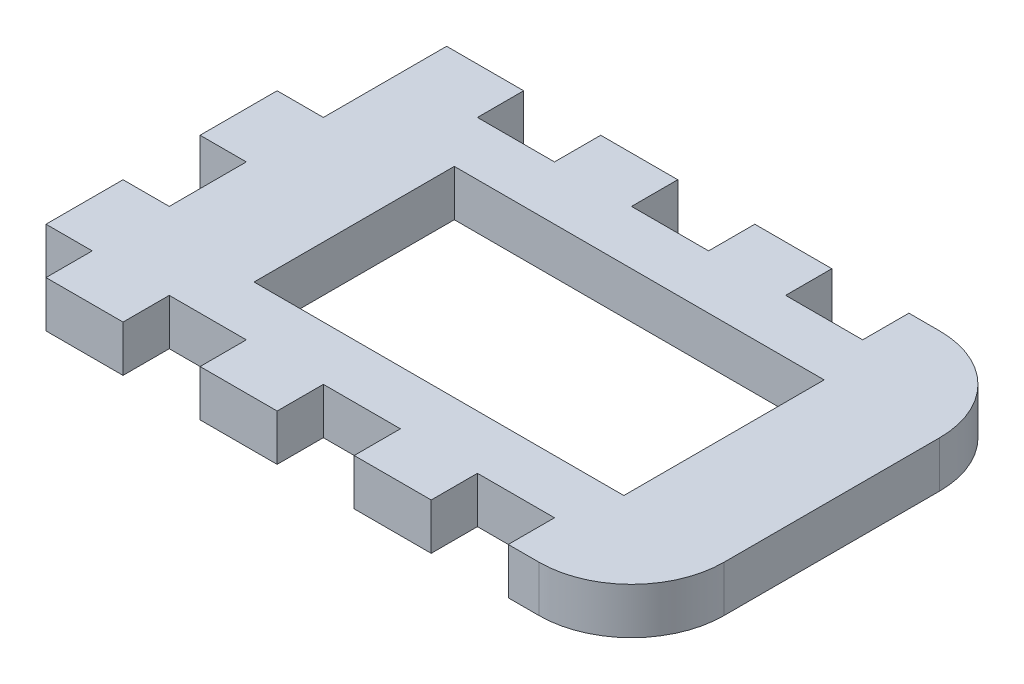
SolidWorks part; units mm, degrees
ref_plane "Front Plane" through (0, 0, 0) normal (0, 0, 1) x (1, 0, 0)
ref_plane "Top Plane" through (0, 0, 0) normal (0, 1, 0) x (1, 0, 0)
ref_plane "Right Plane" through (0, 0, 0) normal (1, 0, 0) x (0, 0, -1)
sketch "Sketch1" plane through (0, 0, 0) normal (0, 1, 0) x (1, 0, 0)
  line L1 (-19, 13) -> (19, 13)
  line L2 (-19, 13) -> (-19, -13)
  line L3 (-19, -13) -> (19, -13)
  line L4 (19, 13) -> (19, -13)
  line L5 (-19, 13) -> (19, -13) construction
  line L6 (-19, -13) -> (19, 13) construction
  point P0 (0, 0)
  dimension "D1" = 38
  dimension "D2" = 26
extrude "Boss-Extrude1" add sketch "Sketch1" along normal mid plane 3
sketch "Sketch2" plane through (0, -1.5, 0) normal (0, -1, 0) x (1, 0, 0)
  line L1 (12, -6.5) -> (-12, -6.5)
  line L2 (12, -6.5) -> (12, 6.5)
  line L3 (12, 6.5) -> (-12, 6.5)
  line L4 (-12, -6.5) -> (-12, 6.5)
  line L5 (12, -6.5) -> (-12, 6.5) construction
  line L6 (12, 6.5) -> (-12, -6.5) construction
  point P0 (0, 0)
  dimension "D1" = 24
  dimension "D2" = 13
extrude "Cut-Extrude1" cut sketch "Sketch2" against normal up to surface (3 mm away) up to face at (0, 1.5, 0)
sketch "Sketch8" plane through (-19, 0, 0) normal (-1, 0, 0) x (0, 0, 1)
  line L0 (-13, -1.5) -> (13, -1.5) construction
  line L1 (-13, 1.5) -> (-10, 1.5)
  line L2 (-13, 1.5) -> (-13, -1.5)
  line L3 (-13, -1.5) -> (-10, -1.5)
  line L4 (-10, 1.5) -> (-10, -1.5)
  line L6 (13, 1.5) -> (10, 1.5)
  line L7 (13, 1.5) -> (13, -1.5)
  line L8 (13, -1.5) -> (10, -1.5)
  line L9 (10, 1.5) -> (10, -1.5)
  line L10 (-10, 1.5) -> (-5, 1.5)
  line L11 (-10, 1.5) -> (-10, -1.5)
  line L12 (-10, -1.5) -> (-5, -1.5)
  line L13 (-5, 1.5) -> (-5, -1.5)
  line L18 (5, 1.5) -> (10, 1.5)
  line L19 (5, 1.5) -> (5, -1.5)
  line L20 (5, -1.5) -> (10, -1.5)
  line L21 (10, 1.5) -> (10, -1.5)
  line L22 (-5, 1.5) -> (0, 1.5)
  line L23 (-5, 1.5) -> (-5, -1.5)
  line L24 (-5, -1.5) -> (0, -1.5)
  line L25 (0, 1.5) -> (0, -1.5)
  line L26 (5, 1.5) -> (0, 1.5)
  line L27 (5, 1.5) -> (5, -1.5)
  line L28 (5, -1.5) -> (0, -1.5)
  line L29 (0, 1.5) -> (0, -1.5)
  line M12 (-13, -1.5) -> (13, -1.5)
  line M14 (13, 1.5) -> (-13, 1.5)
  dimension "D1" = 3
extrude "Boss-Extrude2" add sketch "Sketch8" along normal blind 3 contours L25 L13 M14 M12 | L19 L9 M14 M12 | L22
sketch "Sketch9" plane through (0, -1.5, 0) normal (0, -1, 0) x (1, 0, 0)
  line L0 (-19, 13) -> (19, 13) construction
  line L1 (-14, 13) -> (-19, 13)
  line L2 (-14, 13) -> (-14, 10)
  line L3 (-14, 10) -> (-19, 10)
  line L4 (-19, 13) -> (-19, 10)
  line L5 (-22, 10) -> (-19, 10) construction
  line L6 (-14, 10) -> (-9, 10)
  line L7 (-14, 10) -> (-14, 13)
  line L8 (-14, 13) -> (-9, 13)
  line L9 (-9, 10) -> (-9, 13)
  line L10 (0, 0) -> (-6.2512, 0) construction
  line L11 (-14, -13) -> (-9, -13)
  line L12 (-9, -10) -> (-9, -13)
  line L13 (-14, -10) -> (-9, -10)
  line L14 (-14, -10) -> (-14, -13)
  line L15 (-14, -10) -> (-19, -10)
  line L16 (-19, -13) -> (-19, -10)
  line L17 (-14, -13) -> (-19, -13)
  line L18 (-14, -13) -> (-14, -10)
  line L19 (-4, -10) -> (1, -10)
  line L20 (-9, 13) -> (-4, 13)
  line L21 (-9, 13) -> (-9, 10)
  line L22 (-9, 10) -> (-4, 10)
  line L23 (-4, 13) -> (-4, 10)
  line L24 (-4, 13) -> (1, 13)
  line L25 (-4, 13) -> (-4, 10)
  line L26 (-4, 10) -> (1, 10)
  line L27 (1, 13) -> (1, 10)
  line L28 (1, -13) -> (1, -10)
  line L29 (-4, -13) -> (1, -13)
  line L30 (-4, -13) -> (-4, -10)
  line L31 (-9, -10) -> (-4, -10)
  line L32 (-4, -13) -> (-4, -10)
  line L33 (-9, -13) -> (-4, -13)
  line L34 (-9, -13) -> (-9, -10)
  line L35 (1, -13) -> (6, -13)
  line L36 (1, 10) -> (6, 10)
  line L37 (1, 10) -> (1, 13)
  line L38 (1, 13) -> (6, 13)
  line L39 (6, 10) -> (6, 13)
  line L40 (6, 10) -> (11, 10)
  line L41 (6, 10) -> (6, 13)
  line L42 (6, 13) -> (11, 13)
  line L43 (11, 10) -> (11, 13)
  line L44 (11, 10) -> (16, 10)
  line L45 (11, 10) -> (11, 13)
  line L46 (11, 13) -> (16, 13)
  line L47 (16, 10) -> (16, 13)
  line L48 (6, -10) -> (6, -13)
  line L49 (1, -10) -> (6, -10)
  line L50 (1, -10) -> (1, -13)
  line L51 (6, -13) -> (11, -13)
  line L52 (11, -10) -> (11, -13)
  line L53 (6, -10) -> (11, -10)
  line L54 (6, -10) -> (6, -13)
  line L55 (11, -13) -> (16, -13)
  line L56 (16, -10) -> (16, -13)
  line L57 (11, -10) -> (16, -10)
  line L58 (11, -10) -> (11, -13)
  line M15 (19, 13) -> (-19, 13)
  line M25 (-19, -13) -> (19, -13)
  dimension "D1" = 5
extrude "Cut-Extrude2" cut sketch "Sketch9" against normal up to surface (3 mm away) contours L13 L14 L12 M25 | L6 L9 L2 M15 | L30 L28 L19 M25 | L27 L23 L26 M15 | L53 L48 L52 M25 | L40 L43 L39 M15
fillet "Fillet1" radius 6 2 edges at (19, 0, -13) (19, 0, 13)
